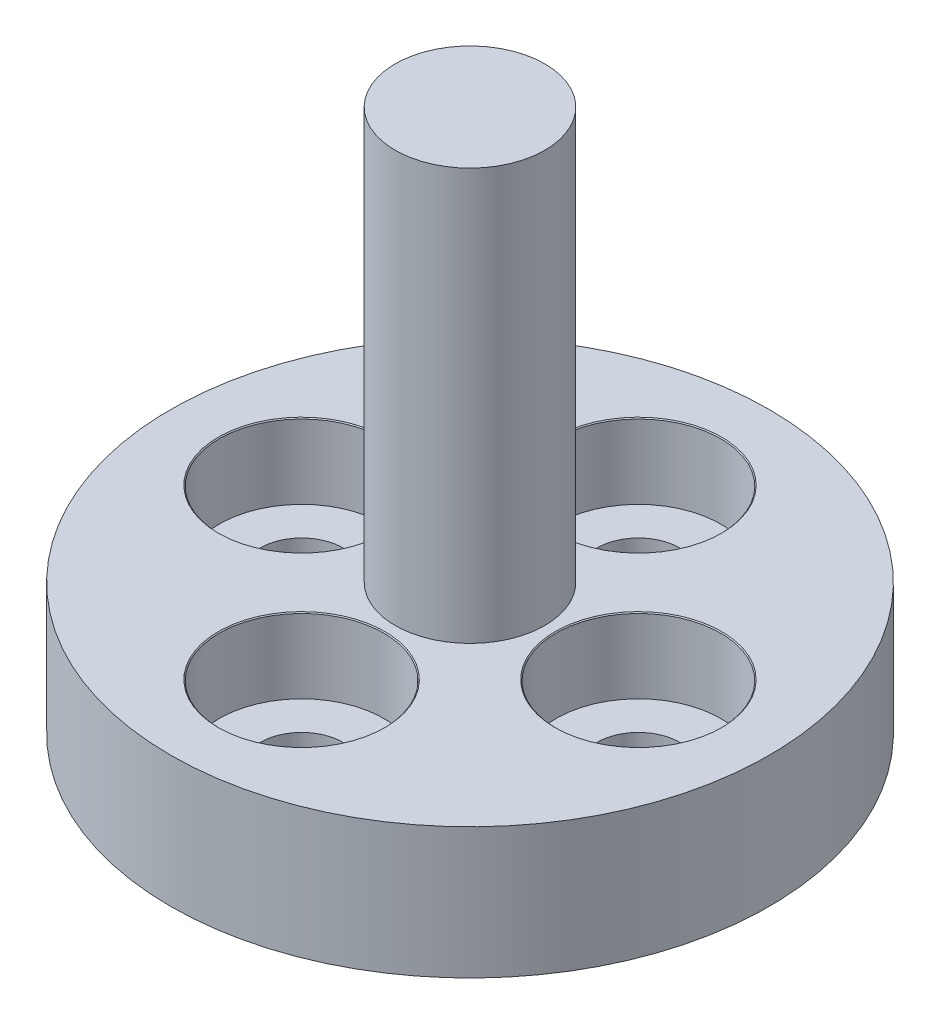
SolidWorks part; units mm, degrees
ref_plane "Front Plane" through (0, 0, 0) normal (0, 0, 1) x (1, 0, 0)
ref_plane "Top Plane" through (0, 0, 0) normal (0, 1, 0) x (1, 0, 0)
ref_plane "Right Plane" through (0, 0, 0) normal (1, 0, 0) x (0, 0, -1)
sketch "Sketch1" plane through (0, 0, 0) normal (0, 0, 1) x (1, 0, 0)
  line L0 (0, 0) -> (0, 14.5)
  line L1 (0, 14.5) -> (2, 14.5)
  line L2 (2, 14.5) -> (2, 3.5)
  line L3 (2, 3.5) -> (8, 3.5)
  line L4 (8, 3.5) -> (8, 0)
  line L5 (8, 0) -> (0, 0)
  dimension "D1" = 8
  dimension "D2" = 2
  dimension "D3" = 14.5
  dimension "D4" = 11
revolve "Revolve1" add sketch "Sketch1" angle 360 about L0
sketch "Sketch2" plane through (0, 14.5, 0) normal (0, 1, 0) x (1, 0, 0)
  circle A0 centre (0, 0) radius 4.5
sketch "Sketch4" plane through (0, 3.5, 0) normal (0, 1, 0) x (1, 0, 0)
  line L0 (-4.5, 0) -> (4.5, 0) construction
  line L2 (0, 4.5) -> (0, -4.5) construction
  circle A0 centre (0, 0) radius 4.5 construction
hole_wizard "CBORE for M2 SHCS1" positions "3DSketch2" profile "Sketch5" counterbore size "M2" standard "ANSI Metric" end condition through all
sketch3d "3DSketch2"
  point P0 (0, 3.5, -4.5)
  point P3 (4.5, 3.5, 0)
  point P6 (0, 3.5, 4.5)
  point P9 (-4.5, 3.5, 0)
sketch "Sketch5" plane through (0, 3.5, -4.5) normal (1, 0, 0) x (0, 0, 1)
  line L0 (0, 0) -> (0, 3.5)
  line L1 (0, 3.5) -> (1.1, 3.5)
  line L3 (1.1, 3.5) -> (1.1, 2)
  line L4 (2.2, 2) -> (1.1, 2)
  line L5 (2.2, 2) -> (2.2, 0.025)
  line L6 (2.2, 0.025) -> (2.225, 0)
  line L7 (2.225, 0) -> (0, 0)
  line L8 (-2.2, 0.025) -> (-2.225, 0) construction
  line L11 (0, -6.35) -> (0, 107.95) construction
  dimension "Thru Hole Dia." = 2.2
  dimension "Thru Hole Depth" = 3.5
  dimension "C'Bore Dia." = 4.4
  dimension "C'Bore Depth" = 2
  dimension "Near C'Sink Dia." = 4.45
  dimension "Near C'Sink Angle" = 90
